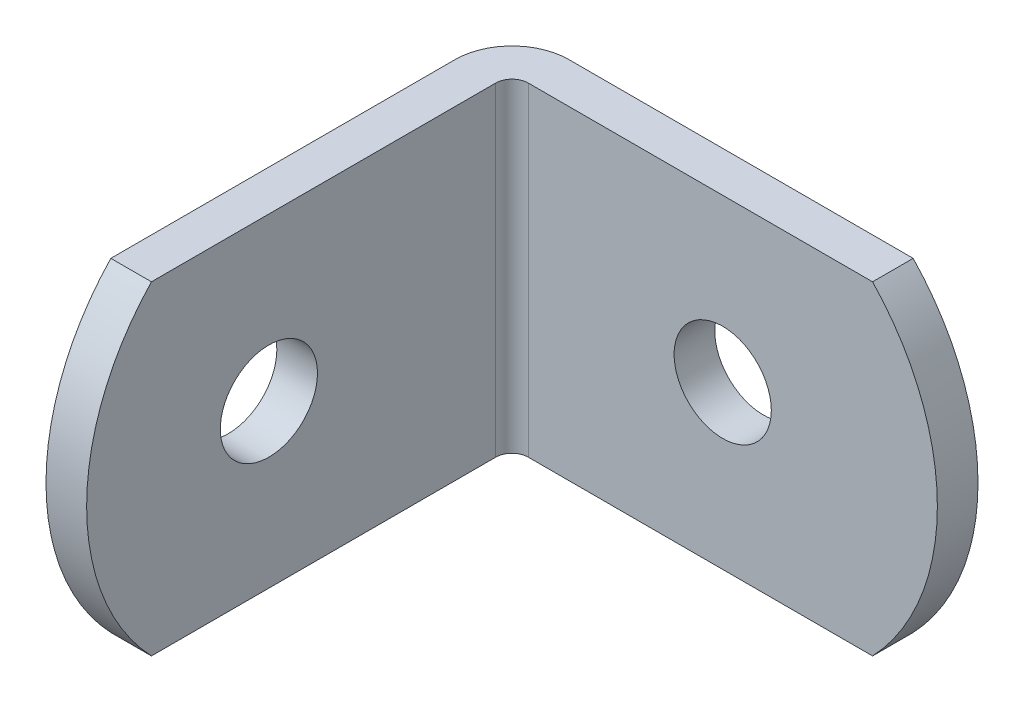
SolidWorks part; units mm, degrees
ref_plane "Front Plane" through (0, 0, 0) normal (0, 0, 1) x (1, 0, 0)
ref_plane "Top Plane" through (0, 0, 0) normal (0, 1, 0) x (1, 0, 0)
ref_plane "Right Plane" through (0, 0, 0) normal (1, 0, 0) x (0, 0, -1)
sketch "Sketch1" plane through (0, 0, 0) normal (0, 1, 0) x (1, 0, 0)
  line L0 (0, -2.8092) -> (0, -23.0124)
  line L1 (2.8092, 0) -> (23.0124, 0)
  line L2 (0, -23.0124) -> (2.0066, -23.0124) construction
  arc A0 (0, -2.8092) -> (2.8092, 0) centre (2.8092, -2.8092) cw
  point P7 (0, 0)
  dimension "D1" = 2.8092
  dimension "Length (A)" = 23.0124
  dimension "Length (B)" = 23.0124
  dimension "Thickness" = 2.0066
sketch "Sketch2" plane through (0, 0, 0) normal (0, 0, 1) x (1, 0, 0)
  line L0 (23.0124, -8.001) -> (23.0124, 8.001) construction
  line L1 (2.8092, 0) -> (23.0124, 0) construction
  circle A0 centre (12.4124, 0) radius 2.4
  arc A1 (19.812, 8.001) -> (19.812, -8.001) centre (11.411, 0) cw
  point P4 (23.0124, 0)
  dimension "Hole Size" = 4.8
  dimension "D2" = 11.6014
  dimension "Length (C)" = 16.002
  dimension "A2 Hole Offset" = 10.6
  dimension "D1" = 3.2004
sketch "Sketch3" plane through (0, 0, 0) normal (1, 0, 0) x (0, 0, -1)
  line L0 (-2.8092, 0) -> (-23.0124, 0) construction
  line L2 (-23.0124, 8.001) -> (-23.0124, -8.001) construction
  line L3 (0, -8.001) -> (0, 8.001) construction
  circle A0 centre (-14.0124, 0) radius 2.4
  arc A1 (-19.812, 8.001) -> (-19.812, -8.001) centre (-11.4109, 0) ccw
  point P14 (-23.0124, 0)
  dimension "D1" = 4.8
  dimension "A1 Hole Offset" = 9
  dimension "D2" = 3.2004
sketch "Sketch4" plane through (0, 0, 0) normal (0, 1, 0) x (1, 0, 0)
  line L0 (0, -2.8092) -> (0, -23.0124) construction
  line L1 (2.8092, 0) -> (23.0124, 0) construction
  line L2 (0, -2.8092) -> (0, -23.0124)
  line L3 (2.8092, 0) -> (23.0124, 0)
  arc A0 (2.8092, 0) -> (0, -2.8092) centre (2.8092, -2.8092) ccw construction
  arc A1 (2.8092, 0) -> (0, -2.8092) centre (2.8092, -2.8092) ccw
extrude "Extrude-Thin1" add sketch "Sketch4" along normal mid plane 16.002 thin thin type one direction wall 2.0066
sketch "Sketch5" plane through (2.0066, 0, 0) normal (1, 0, 0) x (0, 0, -1)
  arc A0 (-19.812, 8.001) -> (-19.812, -8.001) centre (-11.4109, 0) ccw construction
  arc A1 (-19.812, 8.001) -> (-19.812, -8.001) centre (-11.4109, 0) ccw
extrude "Cut-Extrude1" cut sketch "Sketch5" against normal through all and the other way through all flip side to cut
sketch "Sketch7" plane through (2.0066, 0, 0) normal (1, 0, 0) x (0, 0, -1)
  circle A0 centre (-14.0124, 0) radius 2.4 construction
  circle A1 centre (-14.0124, 0) radius 2.4
extrude "Cut-Extrude3" cut sketch "Sketch7" against normal through all
sketch "Sketch6" plane through (0, 0, 2.0066) normal (0, 0, 1) x (1, 0, 0)
  arc A0 (19.812, -8.001) -> (19.812, 8.001) centre (11.411, 0) ccw construction
  arc A1 (19.812, -8.001) -> (19.812, 8.001) centre (11.411, 0) ccw
extrude "Cut-Extrude2" cut sketch "Sketch6" against normal through all and the other way through all flip side to cut
sketch "Sketch8" plane through (0, 0, 2.0066) normal (0, 0, 1) x (1, 0, 0)
  circle A0 centre (12.4124, 0) radius 2.4 construction
  circle A1 centre (12.4124, 0) radius 2.4
extrude "Cut-Extrude4" cut sketch "Sketch8" against normal through all
equation "\"D1@Sketch1\"=\"Thickness@Sketch1\"*1.4"
equation "\"D1@Sketch3\"=\"Hole Size@Sketch2\""
equation "\"D1@Sketch2\"=\"Length (C)@Sketch2\"*.2"
equation "\"D2@Sketch3\"=\"D1@Sketch2\""
equation "\"D5@Extrude-Thin1\"=\"Thickness@sketch1\""
equation "\"D1@Extrude-Thin1\"=\"Length (C)@Sketch2\""
